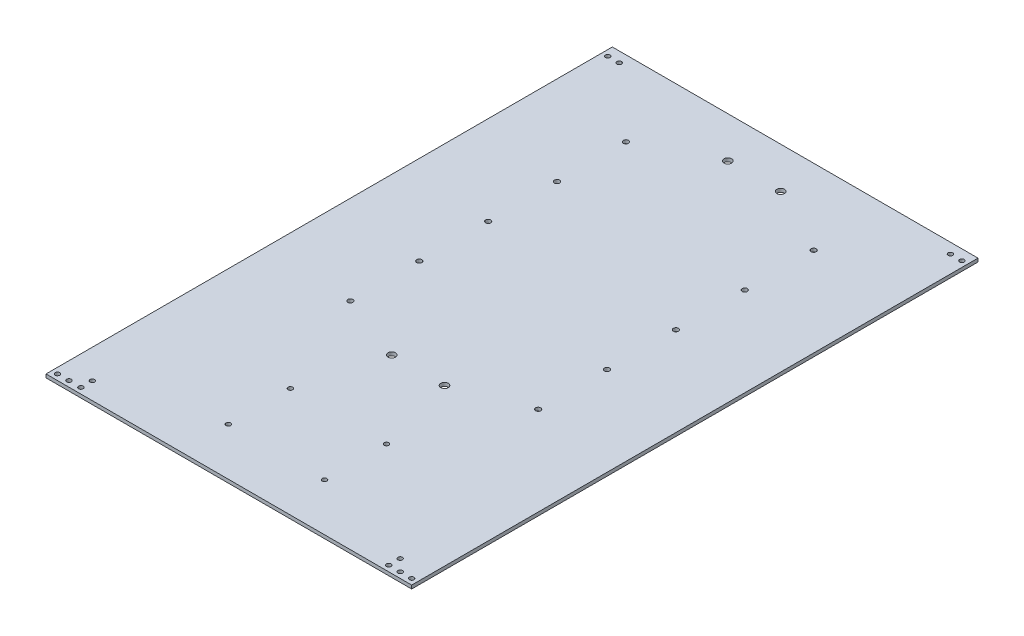
SolidWorks part; units mm, degrees
ref_plane "前视基准面" through (0, 0, 0) normal (0, 0, 1) x (1, 0, 0)
ref_plane "上视基准面" through (0, 0, 0) normal (0, 1, 0) x (1, 0, 0)
ref_plane "右视基准面" through (0, 0, 0) normal (1, 0, 0) x (0, 0, -1)
other "Configuration Table"
sketch "草图1" plane through (0, 0, 0) normal (0, 1, 0) x (1, 0, 0)
  line L1 (-159.28, 246.665) -> (159.28, 246.665)
  line L2 (-159.28, 246.665) -> (-159.28, -246.665)
  line L3 (-159.28, -246.665) -> (159.28, -246.665)
  line L4 (159.28, 246.665) -> (159.28, -246.665)
  line L5 (-159.28, 246.665) -> (159.28, -246.665) construction
  line L6 (-159.28, -246.665) -> (159.28, 246.665) construction
  circle A0 centre (81.78, 181.0128) radius 2.25 construction
  circle A1 centre (81.78, 181.0128) radius 2.25
  circle A2 centre (81.78, 121.0128) radius 2.25 construction
  circle A3 centre (81.78, 121.0128) radius 2.25
  circle A4 centre (81.78, 61.0128) radius 2.25 construction
  circle A5 centre (81.78, 61.0128) radius 2.25
  circle A6 centre (81.78, -58.9872) radius 2.25 construction
  circle A7 centre (81.78, -58.9872) radius 2.25
  circle A8 centre (81.78, 1.0128) radius 2.25 construction
  circle A9 centre (81.78, 1.0128) radius 2.25
  circle A10 centre (-81.78, -58.9872) radius 2.25 construction
  circle A11 centre (-81.78, -58.9872) radius 2.25
  circle A12 centre (-81.78, 1.0128) radius 2.25 construction
  circle A13 centre (-81.78, 1.0128) radius 2.25
  circle A14 centre (-81.78, 61.0128) radius 2.25 construction
  circle A15 centre (-81.78, 61.0128) radius 2.25
  circle A16 centre (-81.78, 121.0128) radius 2.25 construction
  circle A17 centre (-81.78, 121.0128) radius 2.25
  circle A18 centre (-81.78, 181.0128) radius 2.25 construction
  circle A19 centre (-81.78, 181.0128) radius 2.25
  circle A20 centre (-154.28, 237.665) radius 2 construction
  circle A21 centre (-154.28, 237.665) radius 2
  circle A22 centre (-144.28, 237.665) radius 2 construction
  circle A23 centre (-144.28, 237.665) radius 2
  circle A24 centre (144.28, 237.665) radius 2 construction
  circle A25 centre (144.28, 237.665) radius 2
  circle A26 centre (154.28, 237.665) radius 2 construction
  circle A27 centre (154.28, 237.665) radius 2
  circle A28 centre (134.28, -231.665) radius 2 construction
  circle A29 centre (134.28, -231.665) radius 2
  circle A30 centre (134.28, -241.665) radius 2 construction
  circle A31 centre (134.28, -241.665) radius 2
  circle A32 centre (144.28, -241.665) radius 2 construction
  circle A33 centre (144.28, -241.665) radius 2
  circle A34 centre (154.28, -241.665) radius 2 construction
  circle A35 centre (154.28, -241.665) radius 2
  circle A36 centre (-133.8858, -231.665) radius 2 construction
  circle A37 centre (-133.8858, -231.665) radius 2
  circle A38 centre (-133.8858, -241.665) radius 2 construction
  circle A39 centre (-133.8858, -241.665) radius 2
  circle A40 centre (-144.28, -241.665) radius 2 construction
  circle A41 centre (-144.28, -241.665) radius 2
  circle A42 centre (-154.28, -241.665) radius 2 construction
  circle A43 centre (-154.28, -241.665) radius 2
  point P0 (0, 0)
  dimension "D1" = 318.56
  dimension "D2" = 493.33
extrude "凸台-拉伸1" add sketch "草图1" along normal blind 3
sketch "草图2" plane through (0, 0, 0) normal (0, -1, 0) x (1, 0, 0)
  circle A0 centre (41.9, 205.2179) radius 2 construction
  circle A1 centre (41.9, 205.2179) radius 2
  circle A2 centre (-41.9, 151.2179) radius 2 construction
  circle A3 centre (41.9, 151.2179) radius 2 construction
  circle A4 centre (-41.9, 205.2179) radius 2 construction
  circle A5 centre (-41.9, 151.2179) radius 2
  circle A6 centre (41.9, 151.2179) radius 2
  circle A7 centre (-41.9, 205.2179) radius 2
  circle A8 centre (-23, -211.0128) radius 3.3 construction
  circle A9 centre (-23, -211.0128) radius 3.3
  circle A10 centre (23, -211.0128) radius 3.3 construction
  circle A11 centre (23, -211.0128) radius 3.3
  circle A12 centre (-23, 81.7761) radius 3.3 construction
  circle A13 centre (-23, 81.7761) radius 3.3
  circle A14 centre (23, 81.7761) radius 3.3 construction
  circle A15 centre (23, 81.7761) radius 3.3
extrude "切除-拉伸1" cut sketch "草图2" against normal through all both and the other way through all
